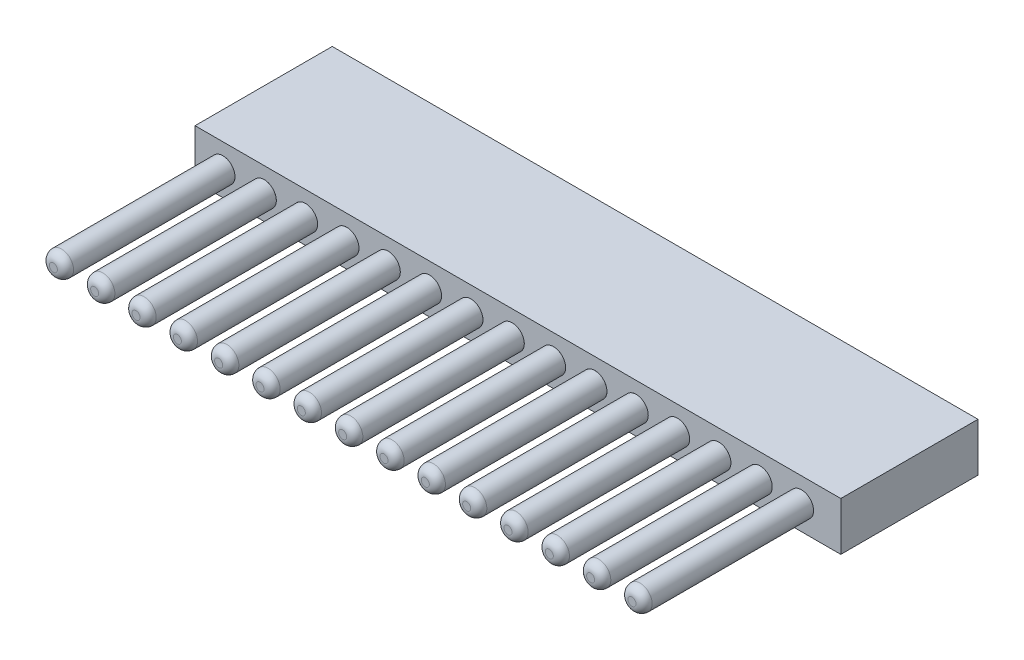
SolidWorks part; units mm, degrees
ref_plane "Front Plane" through (0, 0, 0) normal (0, 0, 1) x (1, 0, 0)
ref_plane "Top Plane" through (0, 0, 0) normal (0, 1, 0) x (1, 0, 0)
ref_plane "Right Plane" through (0, 0, 0) normal (1, 0, 0) x (0, 0, -1)
sketch "Sketch1" plane through (0, 0, 0) normal (0, 0, 1) x (1, 0, 0)
  circle A0 centre (0, 0) radius 0.75
  circle A1 centre (2.56, 0) radius 0.75
  circle A2 centre (5.12, 0) radius 0.75
  circle A3 centre (7.68, 0) radius 0.75
  circle A4 centre (10.24, 0) radius 0.75
  circle A5 centre (12.8, 0) radius 0.75
  circle A6 centre (15.36, 0) radius 0.75
  circle A7 centre (17.92, 0) radius 0.75
  circle A8 centre (20.48, 0) radius 0.75
  circle A9 centre (23.04, 0) radius 0.75
  circle A10 centre (25.6, 0) radius 0.75
  circle A11 centre (28.16, 0) radius 0.75
  circle A12 centre (30.72, 0) radius 0.75
  circle A13 centre (33.28, 0) radius 0.75
  circle A14 centre (35.84, 0) radius 0.75
  dimension "D1" = 1.5
  dimension "D2" = 15
extrude "Boss-Extrude1" add sketch "Sketch1" along normal blind 10.5
fillet "Fillet1" radius 0.5 1 edges at (0.75, 0, 10.5)
sketch "Sketch2" plane through (0, 0, 0) normal (0, 0, -1) x (-1, 0, 0)
  line L0 (1.7251, 0) -> (-38.2749, 0) construction
  line L1 (1.7251, 1.5) -> (-38.2749, 1.5)
  line L2 (1.7251, 1.5) -> (1.7251, -1.5)
  line L3 (1.7251, -1.5) -> (-38.2749, -1.5)
  line L4 (-38.2749, 1.5) -> (-38.2749, -1.5)
  circle A1 centre (-30.72, 0) radius 0.75 construction
  circle A2 centre (-28.16, 0) radius 0.75 construction
  circle A3 centre (-25.6, 0) radius 0.75 construction
  circle A4 centre (-23.04, 0) radius 0.75 construction
  circle A5 centre (-20.48, 0) radius 0.75 construction
  circle A6 centre (-10.24, 0) radius 0.75 construction
  circle A7 centre (-35.84, 0) radius 0.75 construction
  circle A8 centre (-33.28, 0) radius 0.75 construction
  circle A9 centre (-17.92, 0) radius 0.75 construction
  circle A10 centre (-15.36, 0) radius 0.75 construction
  circle A11 centre (-12.8, 0) radius 0.75 construction
  circle A12 centre (-10.24, 0) radius 0.75 construction
  circle A13 centre (-7.68, 0) radius 0.75 construction
  circle A14 centre (-5.12, 0) radius 0.75 construction
  circle A15 centre (-2.56, 0) radius 0.75 construction
  circle A16 centre (0, 0) radius 0.75 construction
  circle A17 centre (-30.72, 0) radius 0.75
  circle A18 centre (-28.16, 0) radius 0.75
  circle A19 centre (-25.6, 0) radius 0.75
  circle A20 centre (-23.04, 0) radius 0.75
  circle A21 centre (-20.48, 0) radius 0.75
  circle A22 centre (-10.24, 0) radius 0.75
  circle A23 centre (-35.84, 0) radius 0.75
  circle A24 centre (-33.28, 0) radius 0.75
  circle A25 centre (-17.92, 0) radius 0.75
  circle A26 centre (-15.36, 0) radius 0.75
  circle A27 centre (-12.8, 0) radius 0.75
  circle A28 centre (-10.24, 0) radius 0.75
  circle A29 centre (-7.68, 0) radius 0.75
  circle A30 centre (-5.12, 0) radius 0.75
  circle A31 centre (-2.56, 0) radius 0.75
  circle A32 centre (0, 0) radius 0.75
  point P6 (0.2434, 0)
  point P8 (-35.84, 0)
  circle M4 centre (0, 0) radius 0.75
  dimension "D1" = 3
  dimension "D2" = 40
extrude "Boss-Extrude2" add sketch "Sketch2" along normal blind 8.5 separate body contours L2 L0 A32 A31 A30 A29 A28 A27 A26 A25 A21 A20 A19 A18 A17 A24 A23 L4 L3 | L0 L2 L1 L4 A23 A24 A17 A18 A19 A20 A21 A25 A26 A27 A22 A29 A30 A31 M4
fillet "Fillet2" radius 0.5 1 edges at (3.31, 0, 10.5)
fillet "Fillet3" radius 0.5 1 edges at (5.87, 0, 10.5)
fillet "Fillet4" radius 0.5 1 edges at (8.43, 0, 10.5)
fillet "Fillet5" radius 0.5 1 edges at (10.99, 0, 10.5)
fillet "Fillet6" radius 0.5 1 edges at (13.55, 0, 10.5)
fillet "Fillet7" radius 0.5 1 edges at (16.11, 0, 10.5)
fillet "Fillet8" radius 0.5 1 edges at (18.67, 0, 10.5)
fillet "Fillet9" radius 0.5 1 edges at (21.23, 0, 10.5)
fillet "Fillet10" radius 0.5 1 edges at (23.79, 0, 10.5)
fillet "Fillet11" radius 0.5 1 edges at (26.35, 0, 10.5)
fillet "Fillet12" radius 0.5 1 edges at (28.91, 0, 10.5)
fillet "Fillet13" radius 0.5 1 edges at (31.47, 0, 10.5)
fillet "Fillet14" radius 0.5 1 edges at (34.03, 0, 10.5)
fillet "Fillet15" radius 0.5 1 edges at (36.59, 0, 10.5)
